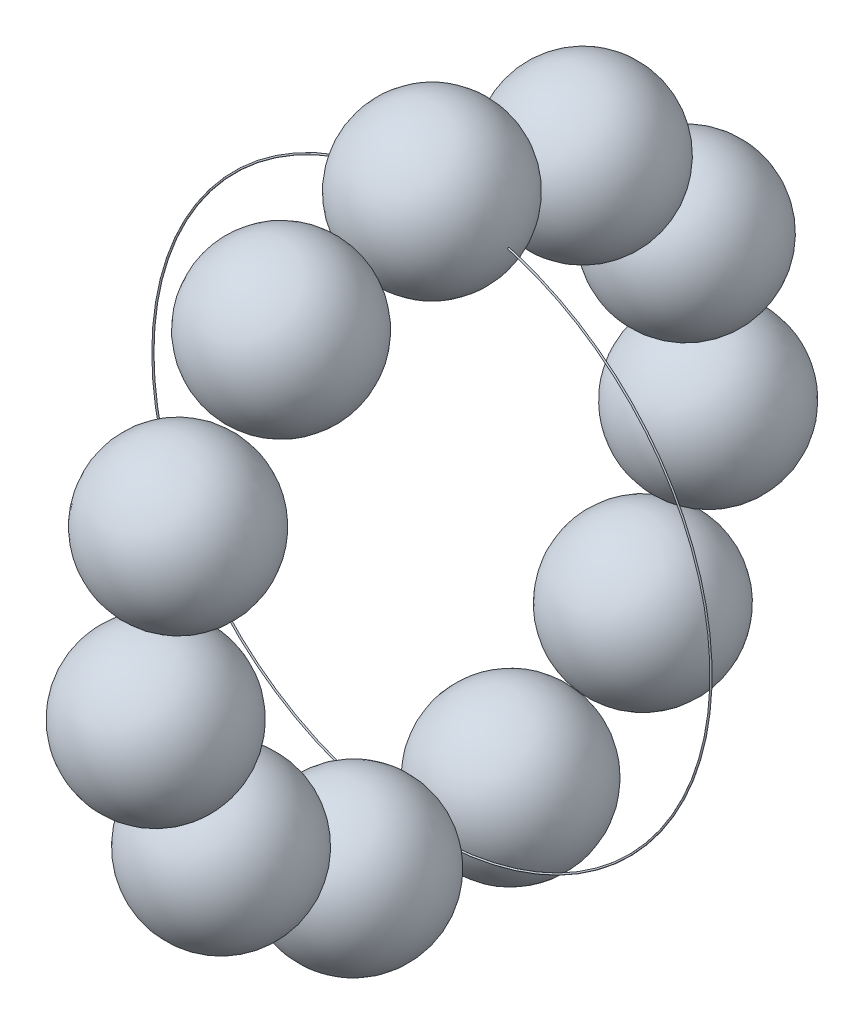
SolidWorks part; units mm, degrees
ref_plane "Alzado" through (0, 0, 0) normal (0, 0, 1) x (1, 0, 0)
ref_plane "Planta" through (0, 0, 0) normal (0, 1, 0) x (1, 0, 0)
ref_plane "Vista lateral" through (0, 0, 0) normal (1, 0, 0) x (0, 0, -1)
sketch "Croquis1" plane through (0, 0, 0) normal (0, 0, 1) x (1, 0, 0)
  line L0 (0, 0) -> (0, 18) construction
  line L1 (0, 23) -> (0, 13)
  arc A0 (0, 13) -> (0, 23) centre (0, 18) ccw
  dimension "D2" = 10
  dimension "D1" = 18
revolve "Revolución1" add sketch "Croquis1" angle 360 about L0
sketch "Croquis4" plane through (0, 0, 0) normal (0, 1, 0) x (1, 0, 0)
  line L0 (0, 0) -> (-18, 0) construction
  line L1 (0, 8.4193) -> (0, -8.9578) construction
  circle A0 centre (-18, 0) radius 0.05
  dimension "D1" = 0.1
  dimension "D2" = 18
revolve "Revolución2" add sketch "Croquis4" angle 360 about L1
sketch "Croquis6" plane through (0, 0, 0) normal (1, 0, 0) x (0, 0, -1)
  line L0 (0, 0) -> (14.2839, 0)
pattern_circular "MatrizC1" count 11 over 360 about axis through (0, 0, 0) along (1, 0, 0) of bodies 101
sketch "Croquis7" plane through (0, 0, 0) normal (1, 0, 0) x (0, 0, -1)
  circle A0 centre (0, 0) radius 18 construction
  dimension "D1" = 36
